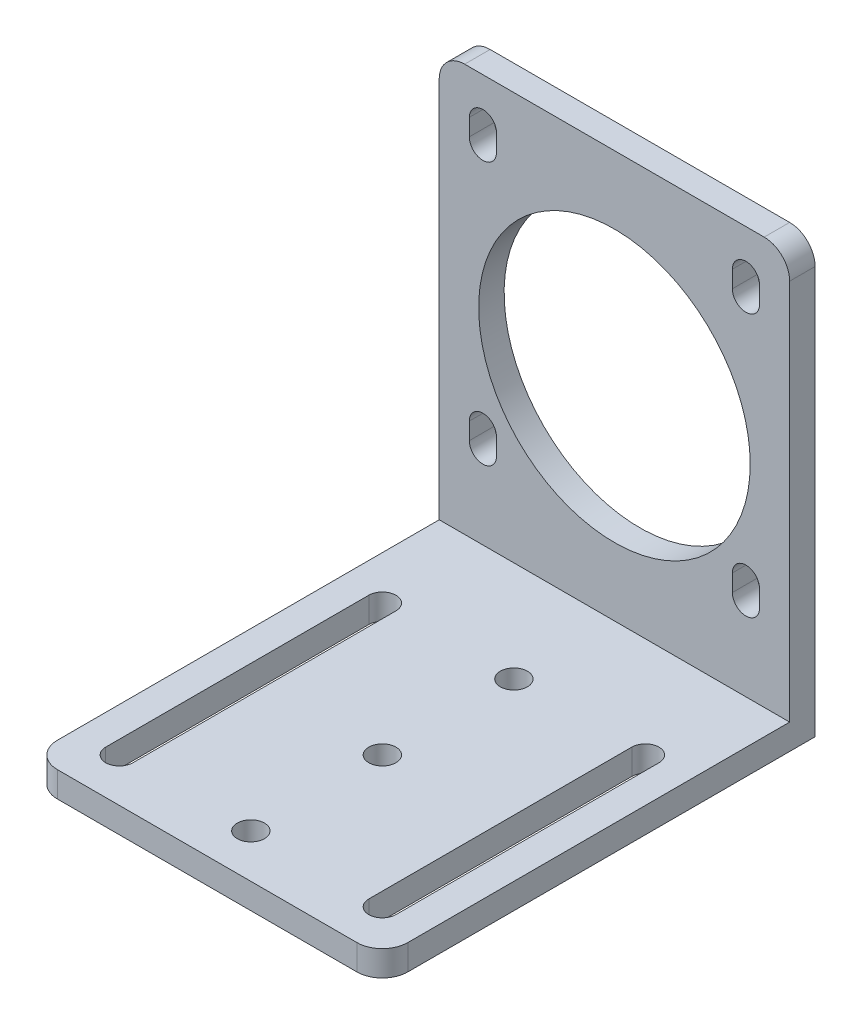
SolidWorks part; units mm, degrees
ref_plane "Front Plane" through (0, 0, 0) normal (0, 0, 1) x (1, 0, 0)
ref_plane "Top Plane" through (0, 0, 0) normal (0, 1, 0) x (1, 0, 0)
ref_plane "Right Plane" through (0, 0, 0) normal (1, 0, 0) x (0, 0, -1)
sketch "Sketch1" plane through (0, 0, 0) normal (1, 0, 0) x (0, 0, -1)
  line L0 (-1.5, -22.5) -> (-49.5, -22.5)
  line L1 (1.5, 25.5) -> (-1.5, 25.5)
  line L2 (1.5, 25.5) -> (1.5, -22.5)
  line L3 (-49.5, -25.5) -> (1.5, -25.5)
  line L4 (-1.5, 25.5) -> (-1.5, -22.5)
  line L5 (1.5, 25.5) -> (0, 0) construction
  line L6 (0, 0) -> (-1.5, 25.5) construction
  line L7 (1.5, -22.5) -> (1.5, -25.5)
  line L8 (1.5, -25.5) -> (1.4268, -25.4395)
  line L10 (-49.5, -25.5) -> (-49.5, -22.5)
  point P0 (0, 0)
  dimension "D1" = 51
  dimension "D2" = 3
  dimension "D3" = 51
  dimension "D4" = 3
extrude "Boss-Extrude1" add sketch "Sketch1" along normal blind 41.3 contours L7 L2 L1 L4 L0 L10 L3
sketch "Sketch2" plane through (0, 0, 1.5) normal (0, 0, 1) x (1, 0, 0)
  line L0 (0, -22.5) -> (41.3, 25.5) construction
  line L1 (0, 25.5) -> (41.3, -22.5) construction
  circle A0 centre (20.65, 1.5) radius 16
  dimension "D1" = 32
sketch "Sketch3" plane through (0, 0, -1.5) normal (0, 0, -1) x (-1, 0, 0)
  line L0 (-41.3, 25.5) -> (0, 25.5) construction
  line L1 (-41.3, 25.5) -> (0, 25.5) construction
  line L2 (-5.15, 46.4502) -> (-5.15, -50.9549) construction
  line L3 (-36.15, 46.4502) -> (-36.15, -50.9549) construction
  point P0 (-5.15, 25.5)
  point P1 (-36.15, 25.5)
  point P4 (-20.65, 25.5)
  point P7 (-20.65, 25.5)
  dimension "D1" = 15.5
  dimension "D2" = 15.5
extrude "Cut-Extrude2" cut sketch "Sketch2" against normal blind 41.3 contours A0
sketch "Sketch4" plane through (0, 0, -1.5) normal (0, 0, -1) x (-1, 0, 0)
  line L0 (-41.3, 25.5) -> (-41.3, -25.5) construction
  line L1 (0, 25.5) -> (0, -25.5) construction
  line L2 (-41.3, 25.5) -> (0, 25.5) construction
  line L3 (-67.3143, 20.35) -> (-6.7575, 20.35) construction
  line L4 (-67.3143, -10.65) -> (-37.75, -10.65) construction
  line L5 (-5.15, 46.4502) -> (-5.15, -50.9549) construction
  line L6 (-3.55, -10.65) -> (36.8895, -10.65) construction
  line L7 (-3.5575, 20.356) -> (-3.55, 18.356)
  line L8 (-6.7575, 20.344) -> (-6.75, 18.344)
  line L9 (-36.15, 20.35) -> (-36.15, 18.35) construction
  line L10 (-36.15, 46.4502) -> (-36.15, -50.9549) construction
  line L11 (-34.55, 20.35) -> (-34.55, 18.35)
  line L12 (-37.75, 20.35) -> (-37.75, 18.35)
  line L13 (-5.15, -10.65) -> (-5.15, -12.65) construction
  line L14 (-3.55, -10.65) -> (-3.55, -12.65)
  line L15 (-6.75, -10.65) -> (-6.75, -12.65)
  line L16 (-36.15, -10.65) -> (-36.15, -12.65) construction
  line L17 (-34.55, -10.65) -> (-34.55, -12.65)
  line L18 (-37.75, -10.65) -> (-37.75, -12.65)
  line L19 (-3.5575, 20.35) -> (36.8895, 20.35) construction
  line L20 (-34.55, -10.65) -> (-6.75, -10.65) construction
  arc A0 (-3.5575, 20.356) -> (-6.7575, 20.344) centre (-5.1575, 20.35) ccw
  arc A1 (-6.75, 18.344) -> (-3.55, 18.356) centre (-5.15, 18.35) ccw
  arc A2 (-34.55, 20.35) -> (-37.75, 20.35) centre (-36.15, 20.35) ccw
  arc A3 (-37.75, 18.35) -> (-34.55, 18.35) centre (-36.15, 18.35) ccw
  arc A4 (-3.55, -10.65) -> (-6.75, -10.65) centre (-5.15, -10.65) ccw
  arc A5 (-6.75, -12.65) -> (-3.55, -12.65) centre (-5.15, -12.65) ccw
  arc A6 (-34.55, -10.65) -> (-37.75, -10.65) centre (-36.15, -10.65) ccw
  arc A7 (-37.75, -12.65) -> (-34.55, -12.65) centre (-36.15, -12.65) ccw
  point P0 (-41.3, 20.35)
  point P1 (0, 20.35)
  point P4 (0, -10.65)
  point P7 (-41.3, -10.65)
  point P19 (-5.1538, 19.35)
  point P28 (-36.15, 19.35)
  point P35 (-5.15, -11.65)
  point P40 (-36.15, -11.65)
  dimension "D5" = 1.6
  dimension "D8" = 1.6
  dimension "D10" = 1.6
  dimension "D12" = 1.6
  dimension "D1" = 5.15
  dimension "D2" = 5.15
  dimension "D3" = 31
  dimension "D4" = 31
  dimension "D6" = 2
  dimension "D7" = 2
  dimension "D9" = 2
  dimension "D11" = 2
extrude "Cut-Extrude7" cut sketch "Sketch4" against normal blind 41.3
sketch "Sketch8" plane through (0, -25.5, 0) normal (0, -1, 0) x (1, 0, 0)
  line L0 (5.15, -1.5) -> (5.15, 52.7289) construction
  line L1 (41.3, -1.5) -> (0, -1.5) construction
  line L2 (36.15, -1.5) -> (36.15, 54.4806) construction
  line L3 (0, 1.5) -> (0, 49.5) construction
  line L4 (41.3, 49.5) -> (41.3, -1.5) construction
  line L5 (-3.1042, 44.35) -> (51.0142, 44.35) construction
  line L6 (0, 13.35) -> (41.3, 13.35) construction
  line L7 (41.3, 49.5) -> (0, 49.5) construction
  line L8 (0, 49.5) -> (0, -1.5) construction
  line L9 (36.15, 44.35) -> (36.15, 13.35) construction
  line L10 (37.75, 44.35) -> (37.75, 13.35)
  line L11 (34.55, 44.35) -> (34.55, 13.35)
  line L12 (5.15, 44.35) -> (5.15, 13.35) construction
  line L13 (6.75, 44.35) -> (6.75, 13.35)
  line L14 (3.55, 44.35) -> (3.55, 13.35)
  line L15 (20.65, 49.5) -> (20.65, 13.35) construction
  arc A0 (37.75, 44.35) -> (34.55, 44.35) centre (36.15, 44.35) ccw
  arc A1 (34.55, 13.35) -> (37.75, 13.35) centre (36.15, 13.35) ccw
  arc A2 (6.75, 44.35) -> (3.55, 44.35) centre (5.15, 44.35) ccw
  arc A3 (3.55, 13.35) -> (6.75, 13.35) centre (5.15, 13.35) ccw
  circle A4 centre (20.65, 44.35) radius 1.6
  circle A5 centre (20.65, 13.35) radius 1.6
  circle A6 centre (20.65, 28.85) radius 1.6
  point P20 (36.15, 28.85)
  point P25 (5.15, 28.85)
  dimension "D5" = 1.6
  dimension "D6" = 1.6
  dimension "D7" = 3.2
  dimension "D8" = 3.2
  dimension "D9" = 3.2
  dimension "D1" = 5.15
  dimension "D2" = 5.15
  dimension "D3" = 5.15
  dimension "D4" = 31
extrude "Cut-Extrude8" cut sketch "Sketch8" against normal blind 41.3
fillet "Fillet1" radius 3 4 edges at (0, -24, 49.5) (41.3, -24, 49.5) (0, 25.5, 0) (41.3, 25.5, 0)
